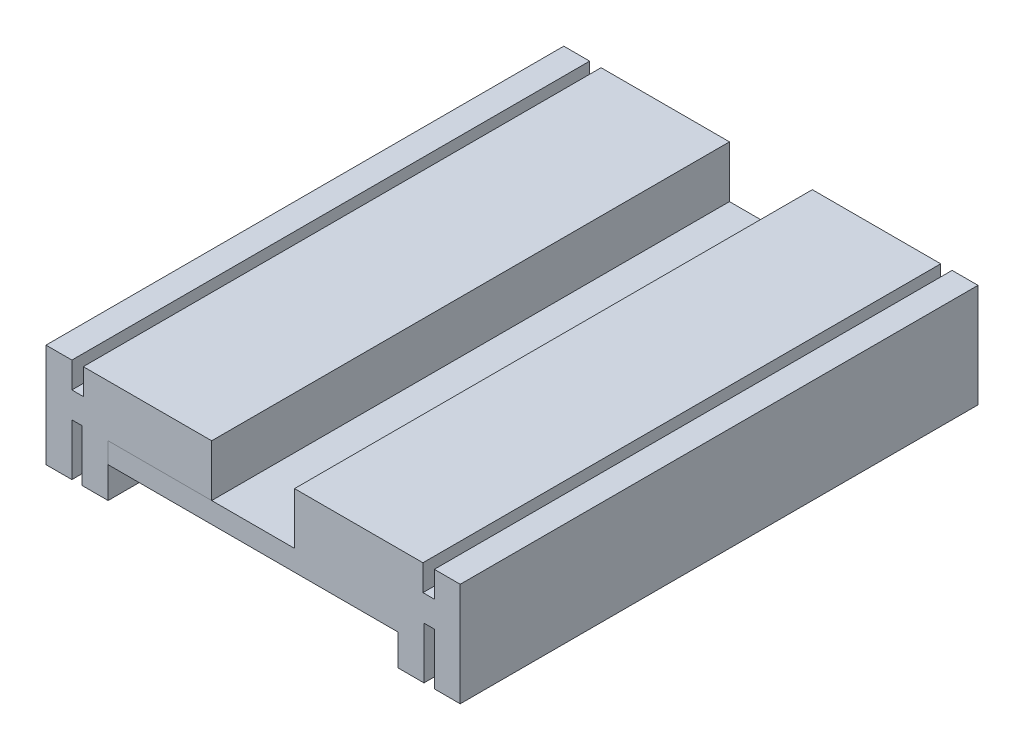
SolidWorks part; units mm, degrees
ref_plane "Plan de face" through (0, 0, 0) normal (0, 0, 1) x (1, 0, 0)
ref_plane "Plan de dessus" through (0, 0, 0) normal (0, 1, 0) x (1, 0, 0)
ref_plane "Plan de droite" through (0, 0, 0) normal (1, 0, 0) x (0, 0, -1)
sketch "Esquisse2" plane through (0, 0, 0) normal (0, 0, 1) x (1, 0, 0)
  line L0 (-40, 0) -> (-10, 0)
  line L2 (-10, 0) -> (10, 0)
  line L4 (10, 0) -> (40, 0)
  dimension "D3" = 10
  dimension "D4" = 10
  dimension "D5" = 30
  dimension "D6" = 30
extrude "Extru.-Mince1" add sketch "Esquisse2" along normal blind 100 thin
sketch "Esquisse4" plane through (0, 0, 0) normal (0, 1, 0) x (1, 0, 0)
  line L0 (-35, 0) -> (-35, -100)
  line L1 (-40, 0) -> (40, 0) construction
  line L2 (-40, -100) -> (40, -100) construction
  line L3 (-35, -100) -> (-32.8, -100)
  line L4 (-32.8, -100) -> (-32.8, 0)
  line L5 (-32.8, 0) -> (-35, 0)
  line L6 (-40, -100) -> (-40, 0) construction
  line L7 (0, 13.4194) -> (0, -107.5339) construction
  line L8 (35, -100) -> (32.8, -100)
  line L9 (32.8, -100) -> (32.8, 0)
  line L10 (35, 0) -> (35, -100)
  line L11 (32.8, 0) -> (35, 0)
  dimension "D1" = 5
  dimension "D2" = 2.2
extrude "Enlèv. mat.-Extru.1" cut sketch "Esquisse4" against normal blind 5
sketch "Esquisse7" plane through (0, -10, 0) normal (0, -1, 0) x (1, 0, 0)
  line L0 (-40, 100) -> (-40, 0)
  line L1 (-40, 0) -> (-35, 0)
  line L2 (-40, 0) -> (40, 0) construction
  line L3 (-35, 0) -> (-35, 100)
  line L4 (-40, 100) -> (40, 100) construction
  line L5 (-35, 100) -> (-40, 100)
  line L6 (-33, 100) -> (-33, 0)
  line L7 (-33, 0) -> (-28, 0)
  line L8 (-28, 0) -> (-28, 100)
  line L9 (-28, 100) -> (-33, 100)
  line L10 (40, 100) -> (40, 0)
  line L11 (40, 0) -> (35, 0)
  line L12 (35, 0) -> (35, 100)
  line L13 (35, 100) -> (40, 100)
  line L14 (33, 100) -> (33, 0)
  line L15 (33, 0) -> (28, 0)
  line L16 (28, 0) -> (28, 100)
  line L17 (28, 100) -> (33, 100)
  dimension "D1" = 5
  dimension "D2" = 2
  dimension "D3" = 5
  dimension "D4" = 5
  dimension "D5" = 2
  dimension "D6" = 5
extrude "Boss.-Extru.1" add sketch "Esquisse7" along normal blind 10
sketch "Esquisse8" plane through (0, 0, 0) normal (0, 1, 0) x (1, 0, 0)
  line L0 (-8, 0) -> (-8, -100)
  line L1 (-32.8, 0) -> (32.8, 0) construction
  line L2 (-32.8, -100) -> (32.8, -100) construction
  line L3 (-8, -100) -> (8, -100)
  line L4 (8, -100) -> (8, 0)
  line L5 (8, 0) -> (-8, 0)
  dimension "D1" = 8
  dimension "D2" = 8
extrude "Enlèv. mat.-Extru.3" cut sketch "Esquisse8" against normal blind 11
sketch "Esquisse9" plane through (0, -10, 0) normal (0, -1, 0) x (1, 0, 0)
  line L0 (-28, 100) -> (28, 100)
  line L1 (28, 100) -> (28, 0)
  line L2 (28, 0) -> (-28, 0)
  line L3 (-28, 0) -> (-28, 100)
extrude "Boss.-Extru.2" add sketch "Esquisse9" along normal blind 4
